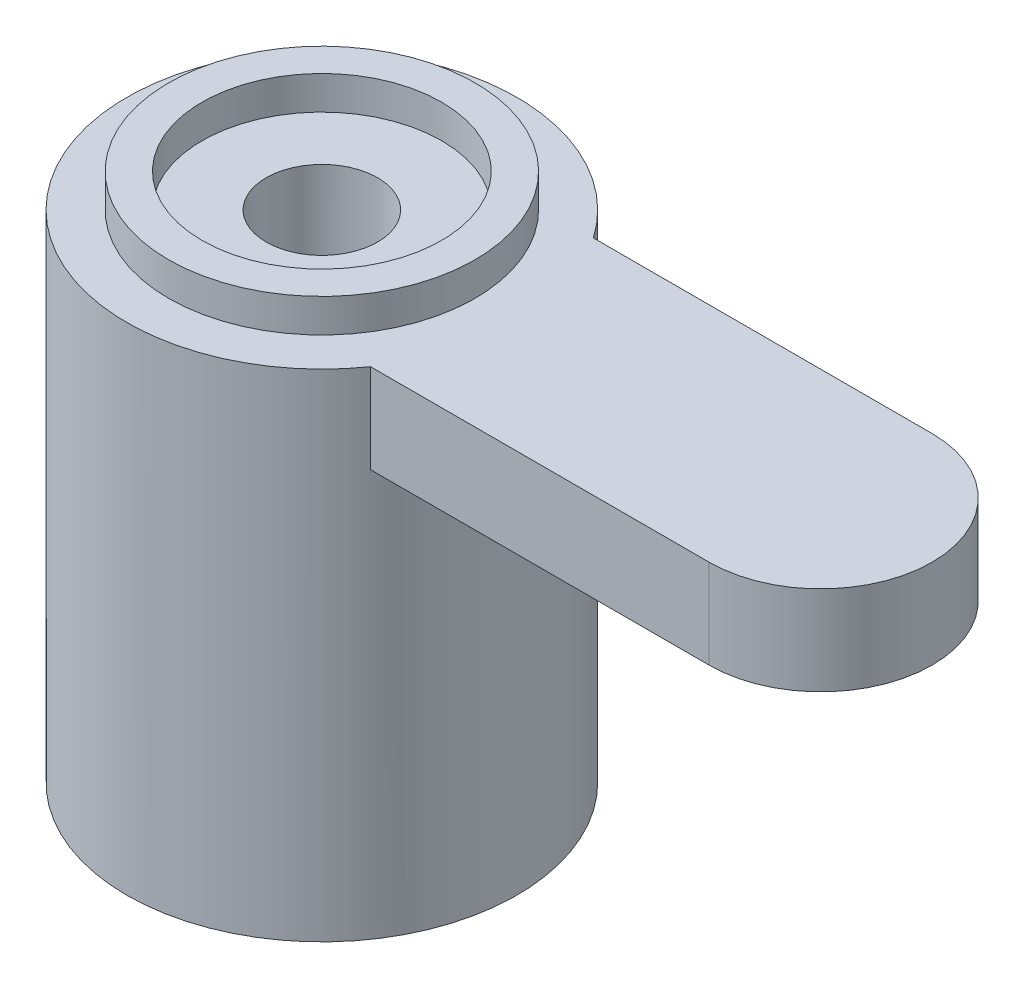
SolidWorks part; units mm, degrees
ref_plane "Płaszczyzna przednia" through (0, 0, 0) normal (0, 0, 1) x (1, 0, 0)
ref_plane "Płaszczyzna górna" through (0, 0, 0) normal (0, 1, 0) x (1, 0, 0)
ref_plane "Płaszczyzna prawa" through (0, 0, 0) normal (1, 0, 0) x (0, 0, -1)
sketch "Szkic1" plane through (0, 0, 0) normal (0, 1, 0) x (1, 0, 0)
  circle A0 centre (0, 0) radius 3.5
  dimension "D1" = 7
extrude "Dodanie-wyciągnięcie1" add sketch "Szkic1" along normal blind 9.5
sketch "Szkic2" plane through (0, 0, 0) normal (0, -1, 0) x (1, 0, 0)
  circle A0 centre (0, 0) radius 1.9
  dimension "D1" = 3.8
extrude "Wytnij-wyciągnięcie1" cut sketch "Szkic2" against normal blind 3.5
ref_plane "Płaszczyzna1" through (0, 8.9, 0) normal (0, 1, 0) x (1, 0, 0)
sketch "Szkic3" plane through (0, 8.9, 0) normal (0, 1, 0) x (1, 0, 0)
  line L0 (0, 0) -> (15.3312, 0) construction
  line L1 (0, 0) -> (0, 11.7192) construction
  line L2 (-8.95, 2) -> (0, 2)
  line L3 (0, 2) -> (8.95, 2)
  line L4 (-8.95, -2) -> (8.95, -2)
  line L5 (-2, -7) -> (-2, 7)
  line L6 (2, -7) -> (2, 0)
  line L7 (2, 0) -> (2, 7)
  circle A0 centre (8.95, 0) radius 2
  circle A1 centre (-8.95, 0) radius 2
  circle A2 centre (0, 7) radius 2
  circle A3 centre (0, -7) radius 2
  dimension "D1" = 4
  dimension "D2" = 4
  dimension "D4" = 4
  dimension "D5" = 4
  dimension "D3" = 17.9
  dimension "D6" = 14
extrude "Dodanie-wyciągnięcie2" add sketch "Szkic3" against normal blind 1.6 contours A1 | A1 L4 L5 L2 | A2 | A2 L5 L2 L3 L7 | A0 L3 L7 L6 L4 | A0 | A3 | A3 L6 L4 L5
sketch "Szkic4" plane through (0, 9.5, 0) normal (0, 1, 0) x (1, 0, 0)
  circle A0 centre (0, 0) radius 2.15
  dimension "D1" = 4.3
extrude "Wytnij-wyciągnięcie2" cut sketch "Szkic4" against normal up to surface (0.6 mm away)
sketch "Szkic5" plane through (0, 8.9, 0) normal (0, 1, 0) x (1, 0, 0)
  circle A0 centre (0, 0) radius 1
  dimension "D1" = 2
extrude "Wytnij-wyciągnięcie3" cut sketch "Szkic5" against normal blind 31.6
sketch "Szkic6" plane through (0, 9.5, 0) normal (0, 1, 0) x (1, 0, 0)
  circle A0 centre (0, 0) radius 3.5 construction
  circle A1 centre (0, 0) radius 2.75
  circle A2 centre (0, 0) radius 3.5
  dimension "D1" = 5.5
extrude "Wytnij-wyciągnięcie4" cut sketch "Szkic6" against normal up to surface (0.6 mm away) up to face at (-6.5681, 8.9, 0)
sketch "Szkic7" plane through (0, 7.3, 0) normal (0, -1, 0) x (1, 0, 0)
  line L0 (2, -2.8723) -> (2, -7) construction
  line L1 (2, 7) -> (2, 2.8723) construction
  line L2 (2, -2.8723) -> (2, -7)
  line L3 (2, 7) -> (2, 2.8723)
  line L4 (2, -7) -> (2, -11.8053)
  line L5 (2, -11.8053) -> (-21.006, -11.8053)
  line L6 (-21.006, -11.8053) -> (-21.006, 11.6684)
  line L7 (-21.006, 11.6684) -> (2, 11.6684)
  line L8 (2, 11.6684) -> (2, 7)
  circle A0 centre (0, 0) radius 3.5 construction
  circle A1 centre (0, 0) radius 3.5
  line M1 (2, -7) -> (2, -2.8723)
  arc M2 (2, -2.8723) -> (-2, -2.8723) centre (0, 0) cw
  line M3 (-2, -2.8723) -> (-2, -7)
  arc M4 (-2, -7) -> (2, -7) centre (0, -7) ccw
extrude "Wytnij-wyciągnięcie5" cut sketch "Szkic7" against normal blind 10 contours M4 M1 M2 M3 | A1 L3 L8 L7 L6 L5 L4 M4 M3
